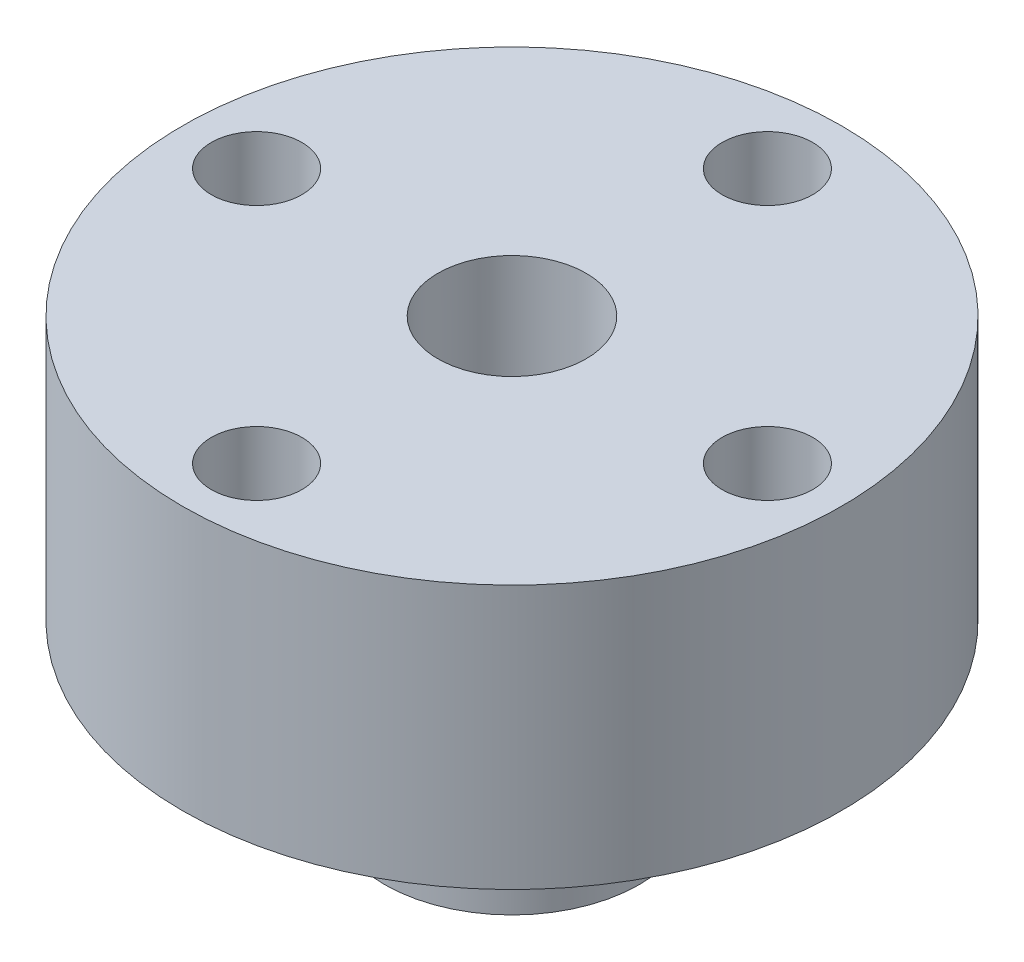
SolidWorks part; units mm, degrees
ref_plane "Front Plane" through (0, 0, 0) normal (0, 0, 1) x (1, 0, 0)
ref_plane "Top Plane" through (0, 0, 0) normal (0, 1, 0) x (1, 0, 0)
ref_plane "Right Plane" through (0, 0, 0) normal (1, 0, 0) x (0, 0, -1)
sketch "Sketch1" plane through (0, 0, 0) normal (0, 1, 0) x (1, 0, 0)
  circle A0 centre (0, 0) radius 3.875
  dimension "D1" = 7.75
extrude "Boss-Extrude1" add sketch "Sketch1" along normal blind 9 and the other way blind 4
sketch "Sketch2" plane through (0, 0, 0) normal (0, 1, 0) x (1, 0, 0)
  circle A0 centre (0, 0) radius 5.4
  dimension "D1" = 10.8
extrude "Boss-Extrude2" add sketch "Sketch2" along normal up to surface (9 mm away) up to face at (0, 9, 3.875)
sketch "Sketch7" plane through (0, 9, 0) normal (0, 1, 0) x (1, 0, 0)
  circle A0 centre (0, 0) radius 10
  dimension "D1" = 20
extrude "Boss-Extrude4" add sketch "Sketch7" against normal blind 8
sketch "Sketch8" plane through (0, -4, 0) normal (0, -1, 0) x (1, 0, 0)
  circle A0 centre (0, 0) radius 2.25
  dimension "D1" = 4.5
extrude "Cut-Extrude4" cut sketch "Sketch8" against normal through all both and the other way through all
sketch "Sketch3" plane through (0, 9, 0) normal (0, 1, 0) x (1, 0, 0)
  circle A0 centre (0, 0) radius 7.75 construction
  circle A1 centre (-7.75, 0) radius 1.375
  dimension "D1" = 15.5
  dimension "D2" = 2.75
extrude "Cut-Extrude2" cut sketch "Sketch3" against normal up to surface (9 mm away) and the other way through all up to face at (0, 0, 3.875)
pattern_circular "CirPattern2" count 4 over 360 about axis through (0, 0, 0) along (0, 1, 0) of "Cut-Extrude2"
